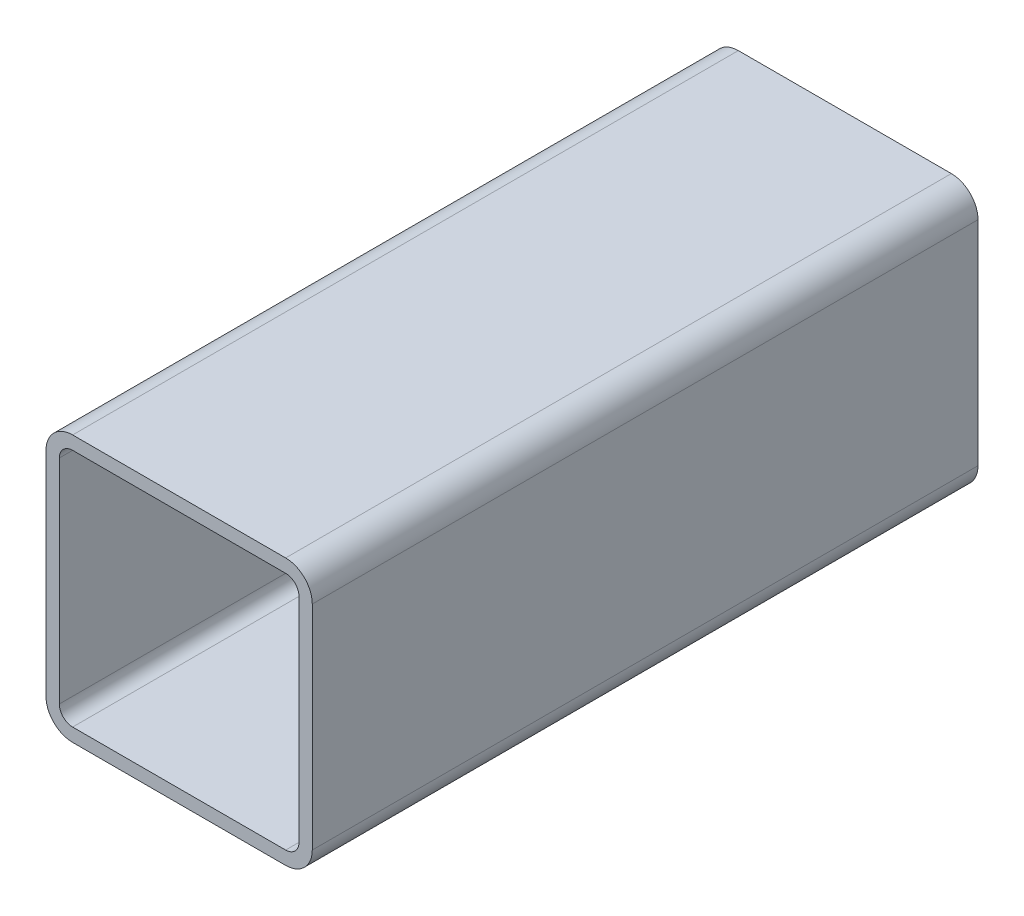
SolidWorks part; units mm, degrees
ref_plane "Front Plane" through (0, 0, 0) normal (0, 0, 1) x (1, 0, 0)
ref_plane "Top Plane" through (0, 0, 0) normal (0, 1, 0) x (1, 0, 0)
ref_plane "Right Plane" through (0, 0, 0) normal (1, 0, 0) x (0, 0, -1)
sketch "Sketch1" plane through (0, 0, 0) normal (0, 0, 1) x (1, 0, 0)
  line L0 (-18, 16) -> (-18, -16)
  line L1 (-16, 20) -> (16, 20)
  line L2 (-20, 16) -> (-20, -16)
  line L3 (-16, -20) -> (16, -20)
  line L4 (20, 16) -> (20, -16)
  line L5 (-20, 20) -> (20, -20) construction
  line L6 (-20, -20) -> (20, 20) construction
  line L7 (-16, -18) -> (16, -18)
  line L8 (18, 16) -> (18, -16)
  line L9 (-16, 18) -> (16, 18)
  arc A0 (-20, 16) -> (-16, 20) centre (-16, 16) cw
  arc A1 (-16, -20) -> (-20, -16) centre (-16, -16) cw
  arc A2 (20, -16) -> (16, -20) centre (16, -16) cw
  arc A3 (20, 16) -> (16, 20) centre (16, 16) ccw
  arc A4 (-16, -18) -> (-18, -16) centre (-16, -16) cw
  arc A5 (18, -16) -> (16, -18) centre (16, -16) cw
  arc A6 (18, 16) -> (16, 18) centre (16, 16) ccw
  arc A7 (-18, 16) -> (-16, 18) centre (-16, 16) cw
  point P0 (0, 0)
  dimension "D1" = 40
  dimension "D3" = 4
  dimension "D2" = 40
  dimension "D4" = 2
extrude "Boss-Extrude1" add sketch "Sketch1" along normal blind 100
sketch "Sketch2" plane through (0, 0, 0) normal (0, 1, 0) x (1, 0, 0)
  line L1 (0, -20) -> (0.1, -20)
  line L2 (0, -20) -> (0, -80)
  line L3 (0, -80) -> (0.1, -80)
  line L4 (0.1, -20) -> (0.1, -80)
  point P4 (0, 0)
  dimension "D1" = 0.1
  dimension "D2" = 20
extrude "Cut-Extrude1" cut sketch "Sketch2" along normal blind 0.5 from surface at -20 contours L2 L3 L4 L1 starting at face at (0, -20, 50)
sketch "Sketch3" plane through (0, 0, 0) normal (0, 1, 0) x (1, 0, 0)
  text T0 "Part1" font "Century Gothic" height 3.5
extrude "Cut-Extrude2" cut sketch "Sketch3" along normal blind 0.5 from surface at -20 starting at face at (0, -20, 50)
